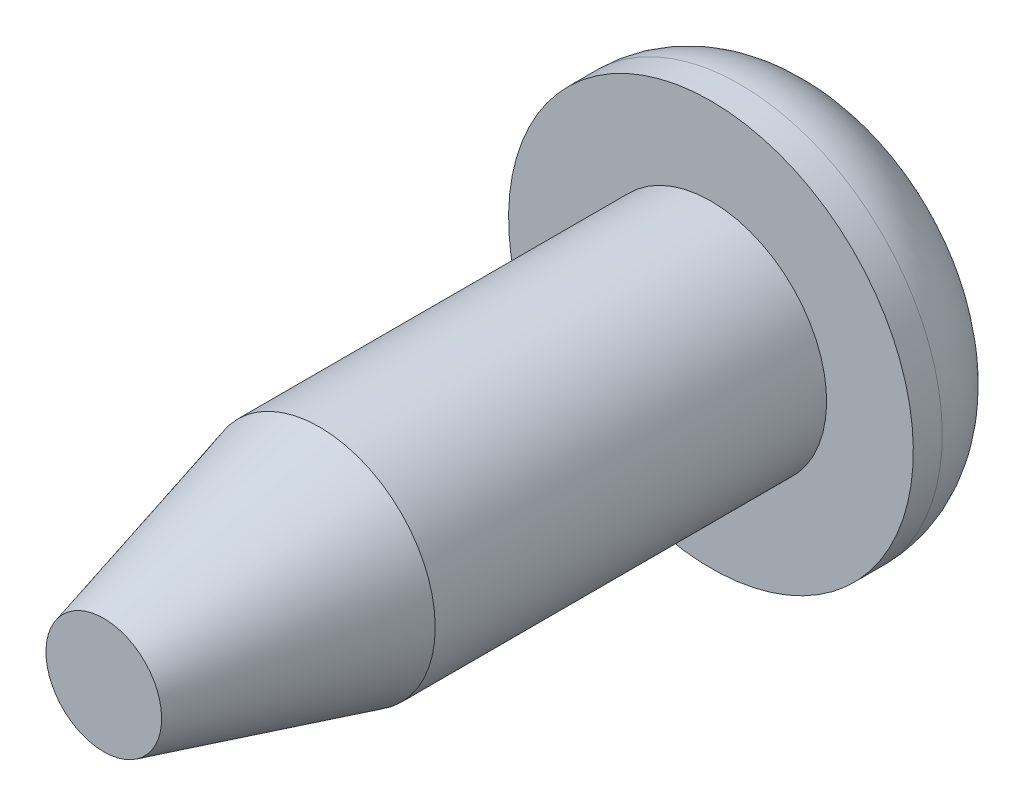
SolidWorks part; units mm, degrees
ref_plane "Front Plane" through (0, 0, 0) normal (0, 0, 1) x (1, 0, 0)
ref_plane "Top Plane" through (0, 0, 0) normal (0, 1, 0) x (1, 0, 0)
ref_plane "Right Plane" through (0, 0, 0) normal (1, 0, 0) x (0, 0, -1)
sketch "Sketch1" plane through (0, 0, 0) normal (1, 0, 0) x (0, 0, -1)
  line L0 (0, 0) -> (-6.35, 0)
  line L1 (-6.35, 0) -> (-6.35, 1.016)
  line L2 (-6.35, 1.016) -> (-1.016, 1.016)
  line L3 (0, 1.016) -> (0, 0)
  line L4 (-1.016, 1.016) -> (-1.016, 1.778)
  line L5 (-1.016, 1.778) -> (-0.762, 1.778)
  arc A0 (0, 1.016) -> (-0.762, 1.778) centre (-0.762, 1.016) ccw
  point P10 (0, 1.778)
  dimension "D4" = 1.778
  dimension "D5" = 0.762
  dimension "D1" = 6.35
  dimension "D2" = 1.016
  dimension "D3" = 1.016
revolve "Revolve1" add sketch "Sketch1" angle 360 about L0
sketch "Sketch2" plane through (0, 0, 0) normal (0, 0, -1) x (-1, 0, 0)
  line L0 (0, 0) -> (-4.882, 0) construction
  line L1 (0, 0) -> (0, 3.2862) construction
  line L2 (0.196, -1.4599) -> (-0.196, -1.4599)
  line L3 (-0.196, -1.4599) -> (-0.196, -0.3488)
  line L4 (-1.4599, 0.196) -> (-0.3488, 0.196)
  line L5 (-1.4599, -0.196) -> (-1.4599, 0.196)
  line L6 (0.196, 1.4599) -> (0.196, 0.3488)
  line L7 (-0.196, 1.4599) -> (0.196, 1.4599)
  line L8 (1.4599, -0.196) -> (0.3488, -0.196)
  line L9 (1.4599, 0.196) -> (1.4599, -0.196)
  line L10 (0.196, -1.4599) -> (0.196, -0.3488)
  line L11 (1.4599, 0.196) -> (0.3488, 0.196)
  line L12 (-1.4599, -0.196) -> (-0.3488, -0.196)
  line L13 (-0.196, 1.4599) -> (-0.196, 0.3488)
  line L14 (-0.3488, 0.196) -> (-0.196, 0.3488)
  line L15 (-0.3488, -0.196) -> (-0.196, -0.3488)
  line L16 (-0.196, -0.3488) -> (-0.2032, -0.353)
  line L17 (0.196, -0.3488) -> (0.3488, -0.196)
  line L18 (0.3488, 0.196) -> (0.196, 0.3488)
  point P10 (0, -1.4599)
  point P21 (0, 0)
  dimension "D1" = 4
extrude "Cut-Extrude1" cut sketch "Sketch2" against normal blind 0.762 contours L3 L2 L10 L17 L8 L9 L11 L18 L6 L7 L13 L14 L4 L5 L12 L15
chamfer "Chamfer1" distance 0.508 angle 75 1 edges at (0, 1.016, 6.35)
